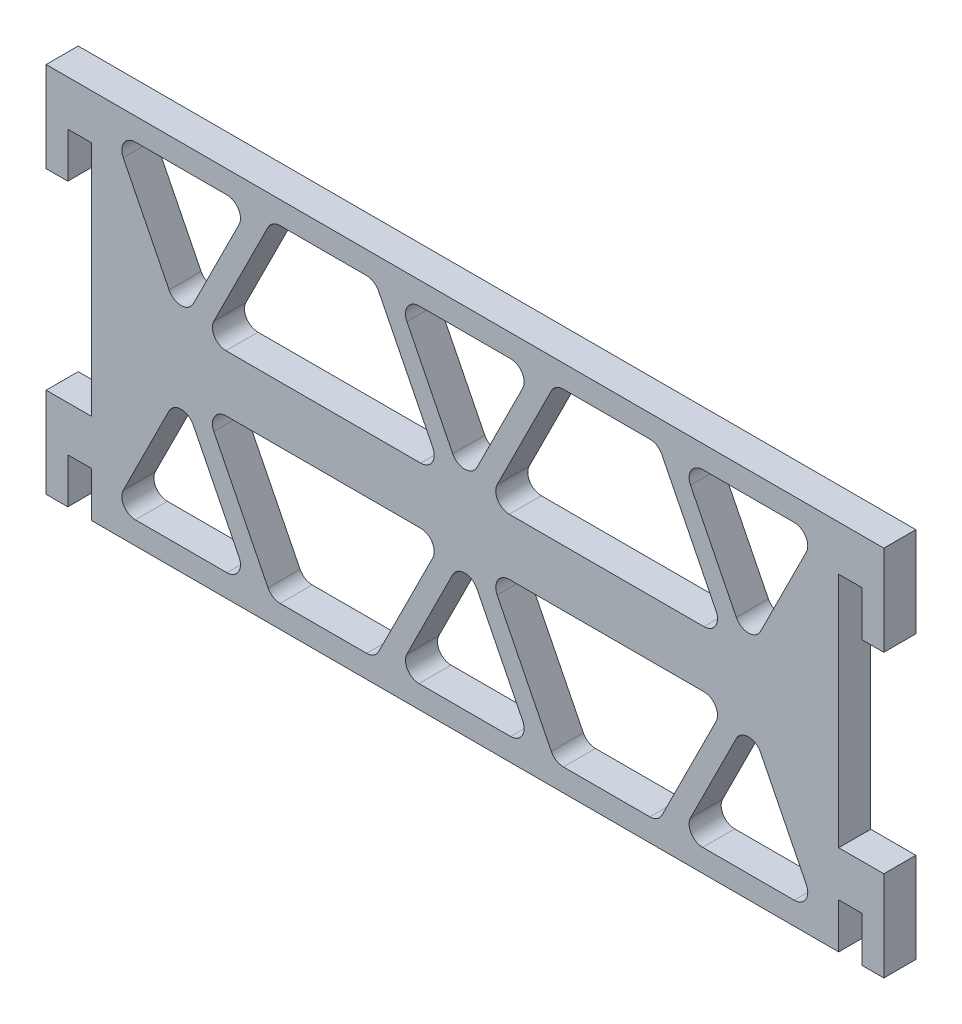
SolidWorks part; units mm, degrees
ref_plane "Front" through (0, 0, 0) normal (0, 0, 1) x (1, 0, 0)
ref_plane "Top" through (0, 0, 0) normal (0, 1, 0) x (1, 0, 0)
ref_plane "Right" through (0, 0, 0) normal (1, 0, 0) x (0, 0, -1)
sketch "Sketch1" plane through (0, 0, 0) normal (0, 0, 1) x (1, 0, 0)
  line L1 (52.5907, -34.1605) -> (-52.5907, -34.1605)
  line L2 (52.5907, -34.1605) -> (52.5907, 34.1605)
  line L3 (52.5907, 34.1605) -> (-52.5907, 34.1605)
  line L4 (-52.5907, -34.1605) -> (-52.5907, 34.1605)
  line L5 (52.5907, -34.1605) -> (-52.5907, 34.1605) construction
  line L6 (52.5907, 34.1605) -> (-52.5907, -34.1605) construction
  point P0 (0, 0)
  dimension "D1" = 105.1814
extrude "Boss-Extrude1" add sketch "Sketch1" along normal blind 4.5085
sketch "Sketch2" plane through (0, 0, 4.5085) normal (0, 0, 1) x (1, 0, 0)
  line L0 (52.5907, -34.1605) -> (52.5907, 34.1605) construction
  line L1 (-52.5907, 34.1605) -> (52.5907, 34.1605)
  line L2 (-52.5907, 34.1605) -> (-52.5907, 18.227)
  line L3 (-52.5907, 18.227) -> (52.5907, 18.227)
  line L4 (52.5907, 34.1605) -> (52.5907, 18.227)
  dimension "D1" = 15.9335
extrude "Cut-Extrude1" cut sketch "Sketch2" against normal blind 10.795
sketch "Sketch3" plane through (0, 0, 4.5085) normal (0, 0, 1) x (1, 0, 0)
  line L0 (-52.5907, 18.227) -> (-52.5907, -34.1605) construction
  line L1 (-52.5907, -34.1605) -> (-58.9407, -34.1605)
  line L2 (-52.5907, -34.1605) -> (-52.5907, -21.4605)
  line L3 (-52.5907, -21.4605) -> (-58.9407, -21.4605)
  line L4 (-58.9407, -34.1605) -> (-58.9407, -21.4605)
  line L5 (-52.5907, 18.227) -> (-58.9407, 18.227)
  line L6 (-52.5907, 18.227) -> (-52.5907, 5.527)
  line L7 (-52.5907, 5.527) -> (-58.9407, 5.527)
  line L8 (-58.9407, 18.227) -> (-58.9407, 5.527)
  dimension "D1" = 6.35
  dimension "D2" = 12.7
  dimension "D3" = 39.6875
  dimension "D4" = 12.7
  dimension "D5" = 6.35
extrude "Boss-Extrude2" add sketch "Sketch3" against normal blind 4.5085
mirror "Mirror1" about plane through (0, 0, 0) normal (1, 0, 0) of "Boss-Extrude2"
sketch "Sketch4" plane through (0, 0, 0) normal (0, 0, -1) x (-1, 0, 0)
  line L0 (-49.4157, 15.052) -> (-30.3657, 15.052)
  line L1 (-30.3657, 15.052) -> (-39.8907, -3.998)
  line L2 (-39.8907, -3.998) -> (-49.4157, 15.052)
  line L3 (58.9407, 18.227) -> (-58.9407, 18.227) construction
  line L4 (-52.5907, -21.4605) -> (-52.5907, 5.527) construction
  dimension "D1" = 19.05
  dimension "D2" = 3.175
  dimension "D3" = 9.525
  dimension "D4" = 19.05
  dimension "D5" = 3.175
extrude "Cut-Extrude2" cut sketch "Sketch4" against normal blind 4.7625
pattern_linear "LPattern1" count 3 spacing 39.9161 along (-1, 0, 0) of "Cut-Extrude2"
sketch "Sketch5" plane through (0, 0, 0) normal (0, 0, -1) x (-1, 0, 0)
  line L0 (-27.1907, 15.052) -> (-12.6746, 15.052)
  line L1 (-12.6746, 15.052) -> (-3.1496, -3.998)
  line L2 (-3.1496, -3.998) -> (-36.7157, -3.998)
  line L3 (-36.7157, -3.998) -> (-27.1907, 15.052)
  line L4 (9.5504, 15.052) -> (-9.4996, 15.052) construction
  dimension "D1" = 3.175
  dimension "D2" = 3.175
  dimension "D3" = 0
  dimension "D4" = 0
  dimension "D5" = 3.175
  dimension "D6" = 3.175
extrude "Cut-Extrude3" cut sketch "Sketch5" against normal blind 4.7625
mirror "Mirror2" about plane through (0, 0, 0) normal (1, 0, 0) of "Cut-Extrude3"
fillet "Fillet2" radius 1.905 9 edges at (-49.4666, 15.052, 2.2542) (-39.9416, -3.998, 2.2542) (-30.4166, 15.052, 2.2542) (-9.5504, 15.052, 2.2542) (9.4996, 15.052, 2.2542) (30.3657, 15.052, 2.2542) (-0.0254, -3.998, 2.2542) (39.8907, -3.998, 2.2542) (49.4157, 15.052, 2.2542)
ref_plane "Plane1" through (0, -7.9667, 0) normal (0, 1, 0) x (1, 0, 0)
mirror "Mirror3" about plane through (0, -7.9667, 0) normal (0, 1, 0) of "LPattern1", "Mirror2", "Cut-Extrude2", "Cut-Extrude3"
fillet "Fillet3" radius 1.905 25 edges at (3.1496, -11.9355, 2.2542) (36.7157, -11.9355, 2.2542) (39.8907, -11.9355, 2.2542) (30.3657, -30.9855, 2.2542) (12.6746, -30.9855, 2.2542) (49.4157, -30.9855, 2.2542) (27.1907, -30.9855, 2.2542) (9.4996, -30.9855, 2.2542) (-0.0254, -11.9355, 2.2542) (-9.5504, -30.9855, 2.2542) (-49.4666, -30.9855, 2.2542) (-30.4166, -30.9855, 2.2542) (-39.9416, -11.9355, 2.2542) (-3.1496, -11.9355, 2.2542) (-12.6746, -30.9855, 2.2542) (-27.1907, -30.9855, 2.2542) (-36.7157, -11.9355, 2.2542) (-36.7157, -3.998, 2.2542) (-3.1496, -3.998, 2.2542) (-27.1907, 15.052, 2.2542) (-12.6746, 15.052, 2.2542) (27.1907, 15.052, 2.2542) (12.6746, 15.052, 2.2542) (3.1496, -3.998, 2.2542) (36.7157, -3.998, 2.2542)
sketch "Sketch6" plane through (0, 0, 0) normal (0, 0, -1) x (-1, 0, 0)
  line L0 (-58.9407, 5.527) -> (-52.5907, 5.527) construction
  line L5 (-52.5907, 5.527) -> (-55.8927, 5.527)
  line L6 (-52.5907, 5.527) -> (-52.5907, 11.877)
  line L7 (-52.5907, 11.877) -> (-55.8927, 11.877)
  line L8 (-55.8927, 5.527) -> (-55.8927, 11.877)
  line L9 (52.5907, 5.527) -> (55.8927, 5.527)
  line L10 (52.5907, 5.527) -> (52.5907, 11.877)
  line L11 (52.5907, 11.877) -> (55.8927, 11.877)
  line L12 (55.8927, 5.527) -> (55.8927, 11.877)
  line L18 (58.9407, -34.1605) -> (-58.9407, -34.1605) construction
  line L19 (-52.5907, -27.8105) -> (-55.8927, -27.8105)
  line L20 (-52.5907, -27.8105) -> (-52.5907, -34.1605)
  line L21 (-52.5907, -34.1605) -> (-55.8927, -34.1605)
  line L22 (-55.8927, -27.8105) -> (-55.8927, -34.1605)
  line L23 (-58.9407, -21.4605) -> (-58.9407, -34.1605) construction
  line L24 (52.5907, -27.8105) -> (55.8927, -27.8105)
  line L25 (52.5907, -27.8105) -> (52.5907, -34.1605)
  line L26 (52.5907, -34.1605) -> (55.8927, -34.1605)
  line L27 (55.8927, -27.8105) -> (55.8927, -34.1605)
  line L28 (58.9407, -21.4605) -> (58.9407, -34.1605) construction
  dimension "D1" = 3.302
  dimension "D2" = 6.35
  dimension "D3" = 3.302
  dimension "D4" = 3.302
  dimension "D5" = 6.35
  dimension "D6" = 3.302
  dimension "D7" = 6.35
  dimension "D8" = 6.35
  dimension "D9" = 3.048
  dimension "D10" = 3.048
extrude "Cut-Extrude4" cut sketch "Sketch6" against normal blind 6.35
